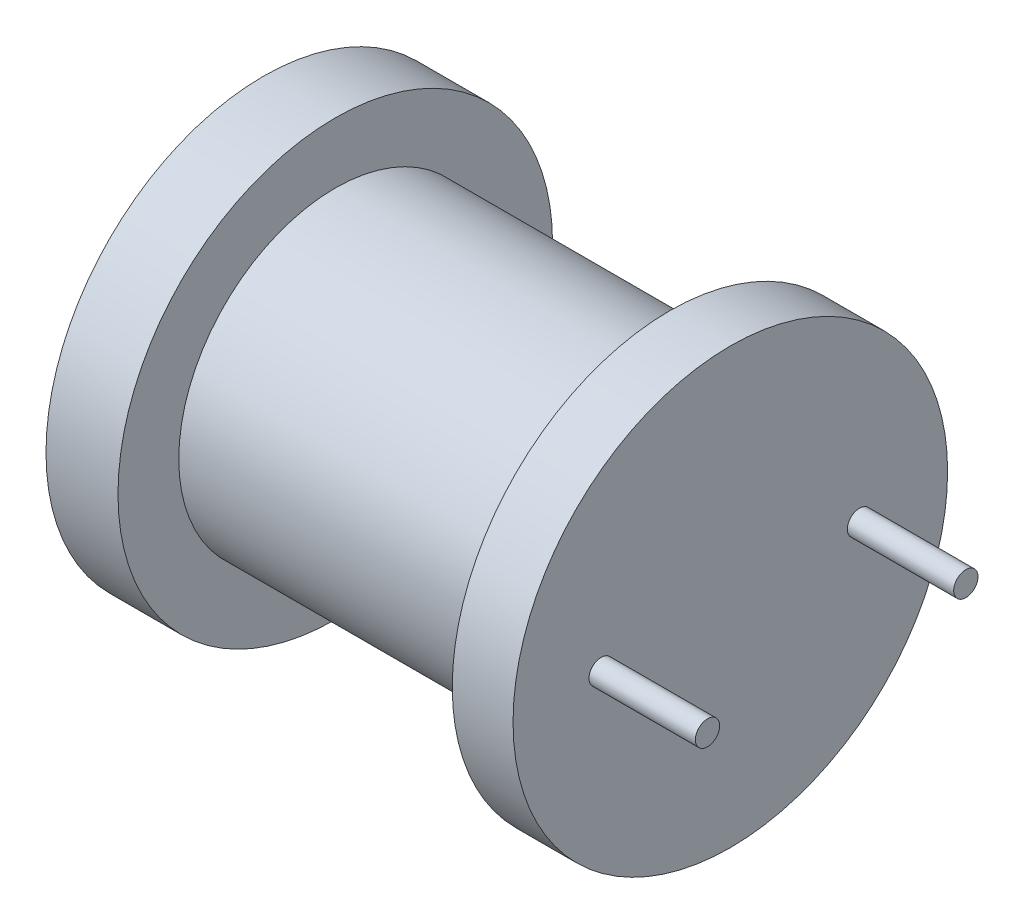
SolidWorks part; units mm, degrees
ref_plane "Спереди" through (0, 0, 0) normal (0, 0, 1) x (1, 0, 0)
ref_plane "Сверху" through (0, 0, 0) normal (0, 1, 0) x (1, 0, 0)
ref_plane "Справа" through (0, 0, 0) normal (1, 0, 0) x (0, 0, -1)
sketch "Эскиз1" plane through (0, 0, 0) normal (0, 0, 1) x (1, 0, 0)
  line L0 (-29.5388, 0) -> (37.4379, 0) construction
  line L1 (0, 15.7651) -> (0, -12.3797) construction
  line L2 (0, 0) -> (0, 7)
  line L3 (0, 7) -> (0.0313, 7.15)
  line L4 (0.0313, 7.15) -> (2.4, 7.15)
  line L5 (2.4, 7.15) -> (2.4, 5.15)
  line L6 (2.4, 5.15) -> (13.4, 5.15)
  line L7 (13.4, 5.15) -> (13.4, 7.15)
  line L8 (13.4, 7.15) -> (15.4, 7.15)
  line L9 (15.4, 7.15) -> (15.4, 0)
  line L10 (15.4, 0) -> (0, 0)
  point P7 (0, 0)
  point P15 (0.0313, 7.15)
  dimension "D1" = 15.4
  dimension "D2" = 7.15
  dimension "D3" = 7
  dimension "D4" = 2
  dimension "D5" = 2
  dimension "D6" = 11
  dimension "D7" = 0.0313
  dimension "D8" = 2
revolve "Повернуть1" add sketch "Эскиз1" angle 360 about L0
sketch "Эскиз2" plane through (15.4, 0, 0) normal (1, 0, 0) x (0, 0, -1)
  circle A0 centre (-4.25, 0) radius 0.4
  circle A1 centre (4.25, 0) radius 0.4
  dimension "D1" = 0.8
  dimension "D2" = 0.8
  dimension "D3" = 4.25
  dimension "D4" = 8.5
extrude "Бобышка-Вытянуть1" add sketch "Эскиз2" along normal blind 3.5
